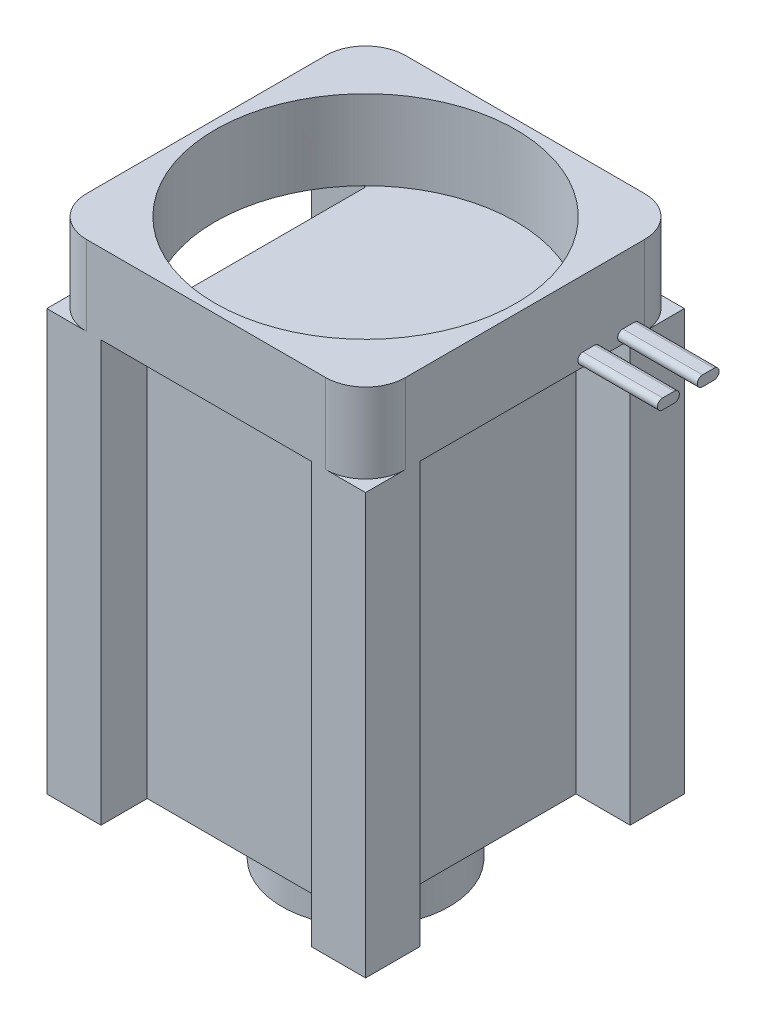
SolidWorks part; units mm, degrees
ref_plane "Front Plane" through (0, 0, 0) normal (0, 0, 1) x (1, 0, 0)
ref_plane "Top Plane" through (0, 0, 0) normal (0, 1, 0) x (1, 0, 0)
ref_plane "Right Plane" through (0, 0, 0) normal (1, 0, 0) x (0, 0, -1)
sketch "Sketch1" plane through (0, 0, 0) normal (0, 1, 0) x (1, 0, 0)
  line L1 (20, 20) -> (-20, 20)
  line L2 (20, 20) -> (20, -20)
  line L3 (20, -20) -> (-20, -20)
  line L4 (-20, 20) -> (-20, -20)
  line L5 (20, 20) -> (-20, -20) construction
  line L6 (20, -20) -> (-20, 20) construction
  point P0 (0, 0)
  dimension "D1" = 40
  dimension "D2" = 40
extrude "Boss-Extrude1" add sketch "Sketch1" along normal blind 62.75
sketch "Sketch2" plane through (0, 62.75, 0) normal (0, 1, 0) x (1, 0, 0)
  line L4 (-20, 20) -> (-20, -20)
  line L5 (-20, -20) -> (20, -20)
  line L6 (20, -20) -> (20, 20)
  line L7 (20, 20) -> (-20, 20)
  line L8 (-20, 15) -> (-20, -15)
  line L9 (-15, -20) -> (15, -20)
  line L10 (20, -15) -> (20, 15)
  line L11 (15, 20) -> (-15, 20)
  circle A0 centre (0, 0) radius 18.875
  arc A1 (-20, -15) -> (-15, -20) centre (-15, -15) ccw
  arc A2 (15, -20) -> (20, -15) centre (15, -15) ccw
  arc A3 (20, 15) -> (15, 20) centre (15, 15) ccw
  arc A4 (-20, 15) -> (-15, 20) centre (-15, 15) cw
  point P19 (0, 0)
  line M1 (-20, 20) -> (-20, -20)
  line M2 (-20, -20) -> (20, -20)
  line M3 (20, -20) -> (20, 20)
  line M4 (20, 20) -> (-20, 20)
  dimension "D1" = 37.75
  dimension "D3" = 5
  dimension "D2" = 0
extrude "Cut-Extrude1" cut sketch "Sketch2" against normal blind 10 contours A0 | A1 M1 M2 | A2 M2 M3 | A3 M3 M4 | A4 M1 M4
sketch "Sketch4" plane through (0, 0, 0) normal (0, -1, 0) x (1, 0, 0)
  circle A0 centre (0, 0) radius 10.5
  dimension "D1" = 21
extrude "Boss-Extrude2" add sketch "Sketch4" along normal blind 7
sketch "Sketch5" plane through (0, 0, 0) normal (0, -1, 0) x (1, 0, 0)
  line L0 (-13.2, 20) -> (-13.2, 14.2)
  line L5 (13.2, -13.2) -> (13.2, 13.2)
  line L6 (-20, 13.2) -> (-13.2, 13.2)
  line L7 (-20, -13.2) -> (-13.2, -13.2)
  line L8 (-20, 20) -> (-20, -20)
  line L9 (-20, -20) -> (20, -20)
  line L10 (20, -20) -> (20, 20)
  line L11 (20, 20) -> (-20, 20)
  line L12 (-20, 13.2) -> (-20, -13.2)
  line L14 (20, -13.2) -> (20, 13.2)
  line L15 (13.2, 20) -> (-13.2, 20)
  line L16 (20, -20) -> (-20, -20) construction
  line L17 (13.2, -13.2) -> (20, -13.2)
  line L18 (-13.2, 14.2) -> (13.2, 14.2)
  line L19 (13.2, 13.2) -> (20, 13.2)
  line L20 (-13.2, 13.2) -> (-13.2, -13.2)
  line L21 (13.2, 14.2) -> (13.2, 20)
  dimension "D2" = 6.8
  dimension "D3" = 6.8
  dimension "D4" = 6.8
  dimension "D5" = 6.8
  dimension "D6" = 1
  dimension "D1" = 0
extrude "Cut-Extrude2" cut sketch "Sketch5" against normal up to surface (52.75 mm away) up to face at (0, 52.75, 18.875)
hole_wizard "M3x0.5 Tapped Hole1" positions "Sketch7" profile "Sketch8" tap size "M3x0.5" standard "ANSI Metric"
sketch "Sketch7" plane through (0, 0, -20) normal (0, 0, -1) x (-1, 0, 0)
  line L0 (0, 35) -> (0, 0) construction
  line L2 (-20, 0) -> (20, 0) construction
  point P0 (-10, 45)
  point P2 (10, 45)
  point P4 (10, 5)
  point P6 (-10, 5)
  point P8 (0, 35)
  point P16 (0, 0)
  point P17 (0, 0)
  point P18 (0, 0)
  point P19 (0, 0)
  point P20 (-9.1943, 44.174)
  dimension "D1" = 20
  dimension "D2" = 40
  dimension "D3" = 10
  dimension "D4" = 5
sketch "Sketch8" plane through (10, 45, -20) normal (1, 0, 0) x (0, 1, 0)
  line L0 (0, 0) -> (0, 5.7511)
  line L1 (0, 5.7511) -> (1.25, 5)
  line L2 (1.25, 5) -> (1.25, 0)
  line L5 (1.25, 0) -> (0, 0)
  line L10 (0, 5.7511) -> (-1.25, 5) construction
  line L11 (0, -6.35) -> (0, 107.95) construction
  dimension "Tap Drill Dia." = 2.5
  dimension "Tap Drill Depth" = 5
  dimension "Drill Angle" = 118
cosmetic thread "Hole Thread1" parameters "D1"=5, "D2"=3
cosmetic thread "Hole Thread2" parameters "D1"=5, "D2"=3
cosmetic thread "Hole Thread3" parameters "D1"=5, "D2"=3
cosmetic thread "Hole Thread4" parameters "D1"=5, "D2"=3
cosmetic thread "Hole Thread5" parameters "D1"=5, "D2"=3
sketch "Sketch9" plane through (20, 0, 0) normal (1, 0, 0) x (0, 0, -1)
  line L0 (7.275, 53.75) -> (8.725, 53.75) construction
  line L1 (7.275, 54.4) -> (8.725, 54.4)
  line L2 (7.275, 53.1) -> (8.725, 53.1)
  line L3 (12.275, 53.75) -> (13.725, 53.75) construction
  line L4 (12.275, 54.4) -> (13.725, 54.4)
  line L5 (12.275, 53.1) -> (13.725, 53.1)
  line L6 (15, 52.75) -> (15, 62.75) construction
  line L7 (-13.2, 52.75) -> (13.2, 52.75) construction
  arc A0 (7.275, 54.4) -> (7.275, 53.1) centre (7.275, 53.75) ccw
  arc A1 (8.725, 53.1) -> (8.725, 54.4) centre (8.725, 53.75) ccw
  arc A2 (12.275, 54.4) -> (12.275, 53.1) centre (12.275, 53.75) ccw
  arc A3 (13.725, 53.1) -> (13.725, 54.4) centre (13.725, 53.75) ccw
  point P2 (8, 53.75)
  point P7 (13, 53.75)
  dimension "D1" = 1.3
  dimension "D2" = 2.75
  dimension "D3" = 5
  dimension "D4" = 2
  dimension "D5" = 1
extrude "Boss-Extrude3" add sketch "Sketch9" along normal blind 10
